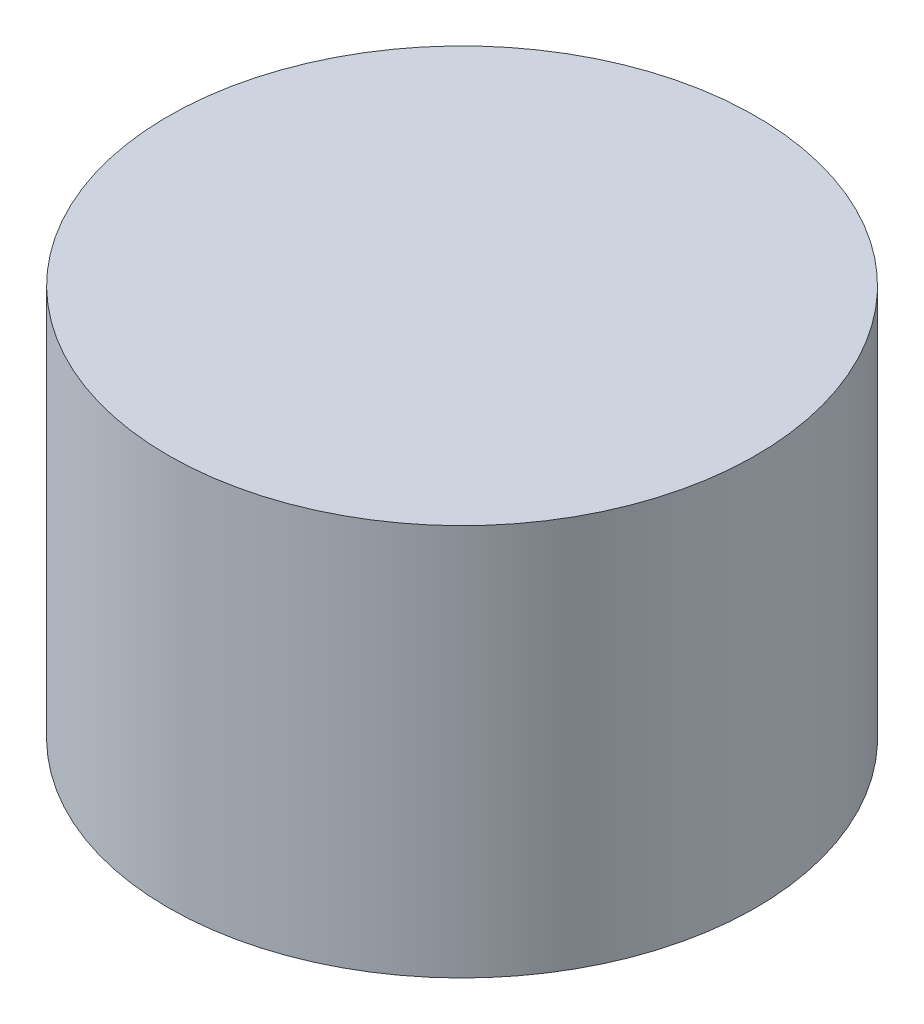
SolidWorks part; units mm, degrees
ref_plane "Front Plane" through (0, 0, 0) normal (0, 0, 1) x (1, 0, 0)
ref_plane "Top Plane" through (0, 0, 0) normal (0, 1, 0) x (1, 0, 0)
ref_plane "Right Plane" through (0, 0, 0) normal (1, 0, 0) x (0, 0, -1)
sketch "Sketch1" plane through (0, 0, 0) normal (0, 1, 0) x (1, 0, 0)
  circle A0 centre (0, 0) radius 3
  dimension "D1" = 6
extrude "Boss-Extrude1" add sketch "Sketch1" along normal blind 4
